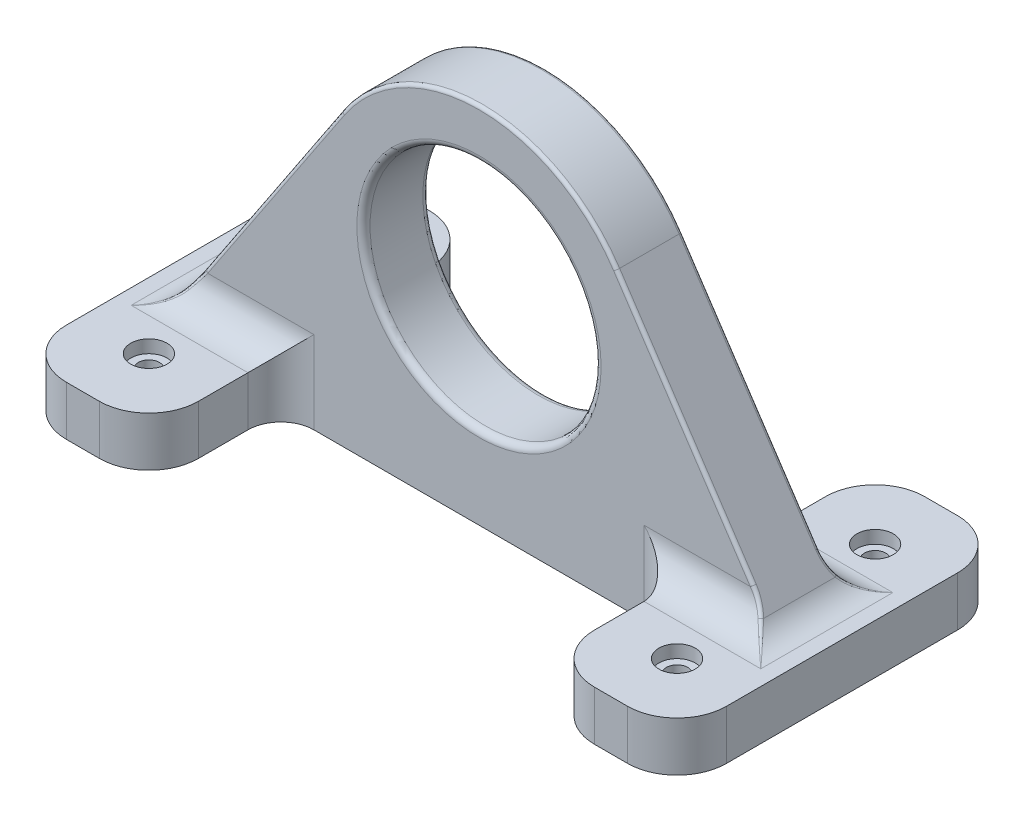
SolidWorks part; units mm, degrees
ref_plane "Front Plane" through (0, 0, 0) normal (0, 0, 1) x (1, 0, 0)
ref_plane "Top Plane" through (0, 0, 0) normal (0, 1, 0) x (1, 0, 0)
ref_plane "Right Plane" through (0, 0, 0) normal (1, 0, 0) x (0, 0, -1)
sketch "Sketch1" plane through (0, 0, 0) normal (0, 0, 1) x (1, 0, 0)
  line L0 (-100, -60) -> (100, -60)
  line L1 (90.0158, -45) -> (41.6228, 27.7046)
  line L2 (-90.0158, -45) -> (-41.6228, 27.7046)
  line L3 (100, -60) -> (100, -45)
  line L4 (100, -45) -> (90.0158, -45)
  line L5 (-100, -45) -> (-100, -60)
  line L6 (-90.0158, -45) -> (-100, -45)
  arc A0 (41.6228, 27.7046) -> (-41.6228, 27.7046) centre (0, 0) ccw
  point P5 (0, -60)
  dimension "D1" = 100
  dimension "D2" = 60
  dimension "D3" = 200
  dimension "D4" = 15
  dimension "D5" = 123.648
extrude "Boss-Extrude1" add sketch "Sketch1" along normal mid plane 20
sketch "Sketch2" plane through (0, 0, 10) normal (0, 0, 1) x (1, 0, 0)
  line L0 (-60, -45) -> (-60, -60)
  line L1 (-100, -45) -> (100, -45)
  line L2 (-100, -45) -> (-100, -60)
  line L3 (-100, -60) -> (100, -60)
  line L4 (100, -45) -> (100, -60)
  line L5 (60, -45) -> (60, -60)
  line M5 (-90.0158, -45) -> (-100, -45)
  line M6 (-100, -45) -> (-100, -60)
  line M7 (-100, -60) -> (100, -60)
  line M8 (100, -60) -> (100, -45)
  line M9 (100, -45) -> (90.0158, -45)
  dimension "D1" = 40
  dimension "D2" = 40
extrude "Boss-Extrude2" add sketch "Sketch2" along normal blind 40 contours L1 L5 L3 M8 M9 | L1 L0 M5 M6 M7
mirror "Mirror2" about plane through (0, 0, 0) normal (0, 0, 1) of "Boss-Extrude2"
sketch "Sketch3" plane through (0, -45, 0) normal (0, 1, 0) x (1, 0, 0)
  line L0 (60, 50) -> (100, 50) construction
  line L2 (60, 50) -> (60, 10) construction
  point P0 (80, 30)
  point P5 (60, 29.0655)
  point P6 (82.1728, 53.7054)
  dimension "D1" = 20
  dimension "D2" = 20
hole_wizard "CBORE for M6 Cheese Slotted Head1" positions "3DSketch1" profile "Sketch4" counterbore size "M6" standard "KS" end condition up to next
sketch3d "3DSketch1"
  point P0 (80, -45, -30)
sketch "Sketch4" plane through (80, -45, -30) normal (1, 0, 0) x (0, 0, 1)
  line L0 (0, 0) -> (0, 15)
  line L1 (0, 15) -> (3.2, 15)
  line L3 (3.2, 15) -> (3.2, 3.9)
  line L4 (3.2, 3.9) -> (5.5, 3.9)
  line L5 (5.5, 3.9) -> (5.5, 0)
  line L7 (5.5, 0) -> (0, 0)
  line L11 (0, -6.35) -> (0, 107.95) construction
  dimension "Thru Hole Dia." = 6.4
  dimension "Thru Hole Depth" = 15
  dimension "C'Bore Dia." = 11
  dimension "C'Bore Depth" = 3.9
mirror "Mirror3" about plane through (0, 0, 0) normal (1, 0, 0) of "CBORE for M6 Cheese Slotted Head1"
mirror "Mirror4" about plane through (0, 0, 0) normal (0, 0, 1) of "Mirror3", "CBORE for M6 Cheese Slotted Head1"
fillet "Fillet1" radius 10 5 edges at (60, -52.5, 10) (75.0079, -45, 10) (90.0158, -45, 0) (60, -52.5, -10) (75.0079, -45, -10)
fillet "Fillet2" radius 15 4 edges at (60, -52.5, 50) (100, -52.5, 50) (60, -52.5, -50) (100, -52.5, -50)
fillet "Fillet3" radius 10 5 edges at (-60, -52.5, -10) (-60, -52.5, 10) (-75.0079, -45, 10) (-90.0158, -45, 0) (-75.0079, -45, -10)
fillet "Fillet4" radius 15 4 edges at (-60, -52.5, 50) (-100, -52.5, 50) (-60, -52.5, -50) (-100, -52.5, -50)
fillet "Fillet5" radius 1 14 edges at (90.6506, -43.815, 15.2782) (85.2862, -37.8943, 10.428) (62.4912, -3.6477, 10) (-90.6506, -43.815, 15.2782) (-85.2862, -37.8943, 10.428) (-62.4912, -3.6477, 10) (90.6506, -43.815, -15.2782) (85.2862, -37.8943, -10.428) (62.4912, -3.6477, -10) (-90.6506, -43.815, -15.2782) (-85.2862, -37.8943, -10.428) (-62.4912, -3.6477, -10) (0, 50, 10) (0, 50, -10)
sketch "Sketch5" plane through (0, 0, -10) normal (0, 0, -1) x (-1, 0, 0)
  circle A0 centre (0, 0) radius 35
  dimension "D1" = 70
extrude "Cut-Extrude1" cut sketch "Sketch5" against normal through all
fillet "Fillet6" radius 2 2 edges at (-35, 0, -10) (35, 0, 10)
